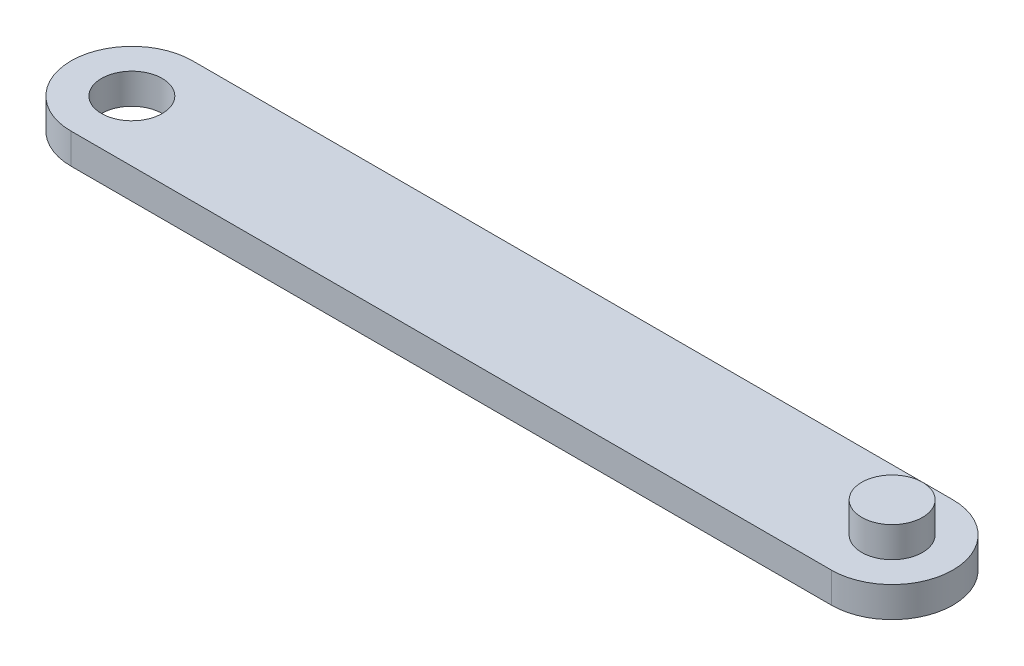
SolidWorks part; units mm, degrees
ref_plane "Front Plane" through (0, 0, 0) normal (0, 0, 1) x (1, 0, 0)
ref_plane "Top Plane" through (0, 0, 0) normal (0, 1, 0) x (1, 0, 0)
ref_plane "Right Plane" through (0, 0, 0) normal (1, 0, 0) x (0, 0, -1)
sketch "Sketch1" plane through (0, 0, 0) normal (0, 1, 0) x (1, 0, 0)
  line L0 (-12.5, 0) -> (12.5, 0) construction
  line L1 (-12.5, 2) -> (12.5, 2)
  line L2 (-12.5, -2) -> (12.5, -2)
  arc A0 (-12.5, 2) -> (-12.5, -2) centre (-12.5, 0) ccw
  arc A1 (12.5, -2) -> (12.5, 2) centre (12.5, 0) ccw
  circle A2 centre (-12.5, 0) radius 1
  circle A3 centre (12.5, 0) radius 1
  point P3 (0, 0)
  dimension "D2" = 2
  dimension "D3" = 2
  dimension "D1" = 25
  dimension "D4" = 4
extrude "Boss-Extrude3" add sketch "Sketch1" along normal blind 1
sketch "Sketch3" plane through (0, 1, 0) normal (0, 1, 0) x (1, 0, 0)
  circle A0 centre (12.5, 0) radius 1
  dimension "D1" = 2
extrude "Boss-Extrude4" add sketch "Sketch3" along normal mid plane 2
sketch "Sketch4" plane through (0, 1, 0) normal (0, 1, 0) x (1, 0, 0)
  circle A0 centre (12.5, 0) radius 1
extrude "Boss-Extrude5" add sketch "Sketch4" along normal blind 1
